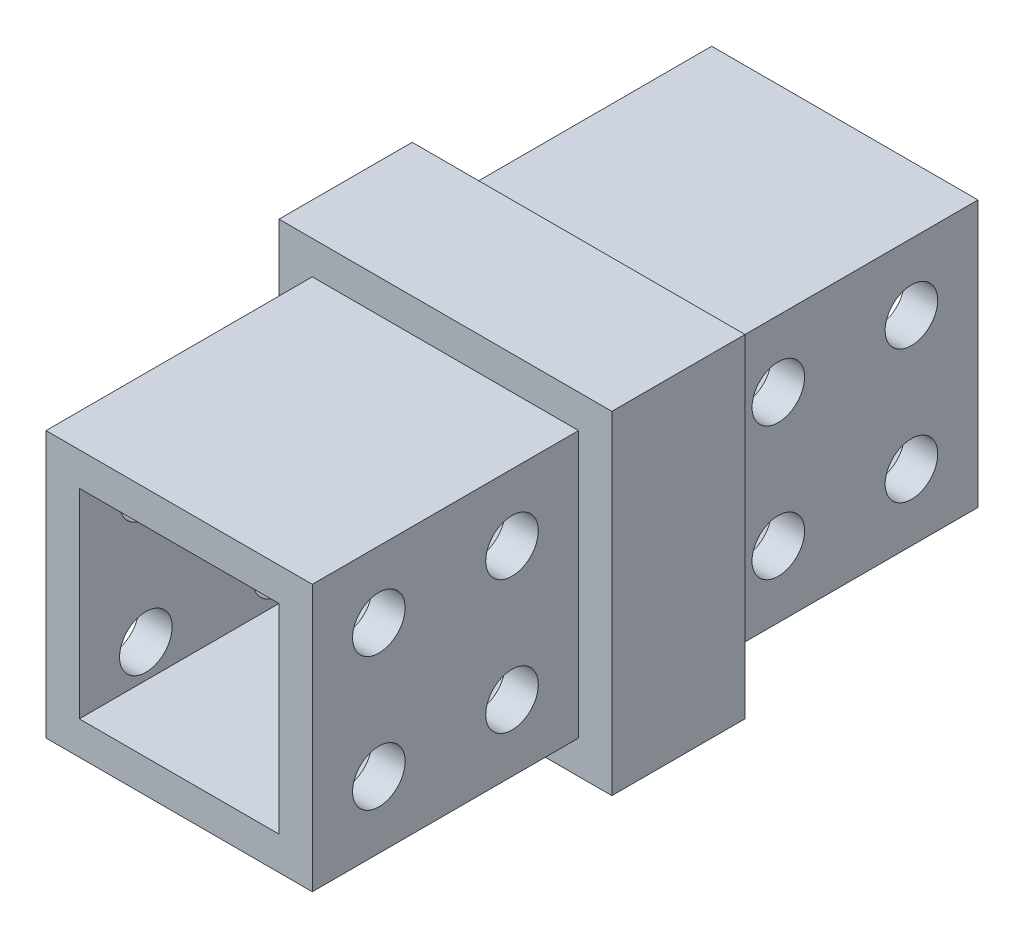
SolidWorks part; units mm, degrees
material "6061-T6 (SS)"
ref_plane "Front Plane" through (0, 0, 0) normal (0, 0, 1) x (1, 0, 0)
ref_plane "Top Plane" through (0, 0, 0) normal (0, 1, 0) x (1, 0, 0)
ref_plane "Right Plane" through (0, 0, 0) normal (1, 0, 0) x (0, 0, -1)
sketch "Sketch1" plane through (0, 0, 0) normal (0, 0, 1) x (1, 0, 0)
  line L1 (0, 0) -> (-25.4, 0)
  line L2 (0, 0) -> (0, -25.4)
  line L3 (0, -25.4) -> (-25.4, -25.4)
  line L4 (-25.4, 0) -> (-25.4, -25.4)
  dimension "D1" = 25.4
  dimension "D2" = 25.4
extrude "Boss-Extrude1" add sketch "Sketch1" along normal blind 25.4
sketch "Sketch2" plane through (0, 0, 25.4) normal (0, 0, 1) x (1, 0, 0)
  line L1 (-28.575, 3.175) -> (3.175, 3.175)
  line L2 (-28.575, 3.175) -> (-28.575, -28.575)
  line L3 (-28.575, -28.575) -> (3.175, -28.575)
  line L4 (3.175, 3.175) -> (3.175, -28.575)
  line L5 (0, 0) -> (-25.4, 0) construction
  line L6 (0, -25.4) -> (0, 0) construction
  dimension "D1" = 31.75
  dimension "D2" = 31.75
  dimension "D3" = 3.175
  dimension "D4" = 3.175
extrude "Boss-Extrude2" add sketch "Sketch2" along normal blind 12.7
sketch "Sketch3" plane through (0, 0, 38.1) normal (0, 0, 1) x (1, 0, 0)
  line L1 (-25.4, 0) -> (0, 0)
  line L2 (-25.4, 0) -> (-25.4, -25.4)
  line L3 (-25.4, -25.4) -> (0, -25.4)
  line L4 (0, 0) -> (0, -25.4)
  line L5 (-28.575, 3.175) -> (-28.575, -28.575) construction
  line L6 (3.175, 3.175) -> (-28.575, 3.175) construction
  dimension "D1" = 25.4
  dimension "D2" = 25.4
  dimension "D3" = 3.175
  dimension "D4" = 3.175
extrude "Boss-Extrude3" add sketch "Sketch3" along normal blind 25.4
sketch "Sketch4" plane through (0, 0, 0) normal (1, 0, 0) x (0, 0, -1)
  line L0 (-63.5, -25.4) -> (-63.5, 0) construction
  line L1 (-63.5, -25.4) -> (-38.1, -25.4) construction
  circle A0 centre (-57.15, -6.35) radius 2.5083
  circle A1 centre (-44.45, -6.35) radius 2.5083
  circle A2 centre (-57.15, -19.05) radius 2.5082
  circle A3 centre (-44.45, -19.05) radius 2.5083
  point P8 (-50.8, -12.7)
  dimension "D1" = 5.0165
  dimension "D2" = 12.7
  dimension "D3" = 12.7
  dimension "D4" = 6.35
  dimension "D5" = 6.35
  dimension "D6" = 6.35
  dimension "D7" = 6.35
  dimension "D8" = 6.35
  dimension "D9" = 6.35
  dimension "D10" = 6.35
  dimension "D11" = 6.35
extrude "Cut-Extrude2" cut sketch "Sketch4" against normal blind 25.4
sketch "Sketch5" plane through (0, 0, 63.5) normal (0, 0, 1) x (1, 0, 0)
  line L0 (0, 0) -> (-25.4, 0) construction
  line L1 (-22.225, -3.175) -> (-3.175, -3.175)
  line L2 (-22.225, -3.175) -> (-22.225, -22.225)
  line L3 (-22.225, -22.225) -> (-3.175, -22.225)
  line L4 (-3.175, -3.175) -> (-3.175, -22.225)
  line L5 (0, -25.4) -> (0, 0) construction
  dimension "D1" = 19.05
  dimension "D2" = 19.05
  dimension "D3" = 3.175
  dimension "D4" = 3.175
extrude "Cut-Extrude3" cut sketch "Sketch5" against normal blind 63.5
ref_plane "Plane1" through (0, 0, 31.75) normal (0, 0, 1) x (1, 0, 0)
mirror "Mirror1" about plane through (0, 0, 31.75) normal (0, 0, 1) of "Cut-Extrude2"
